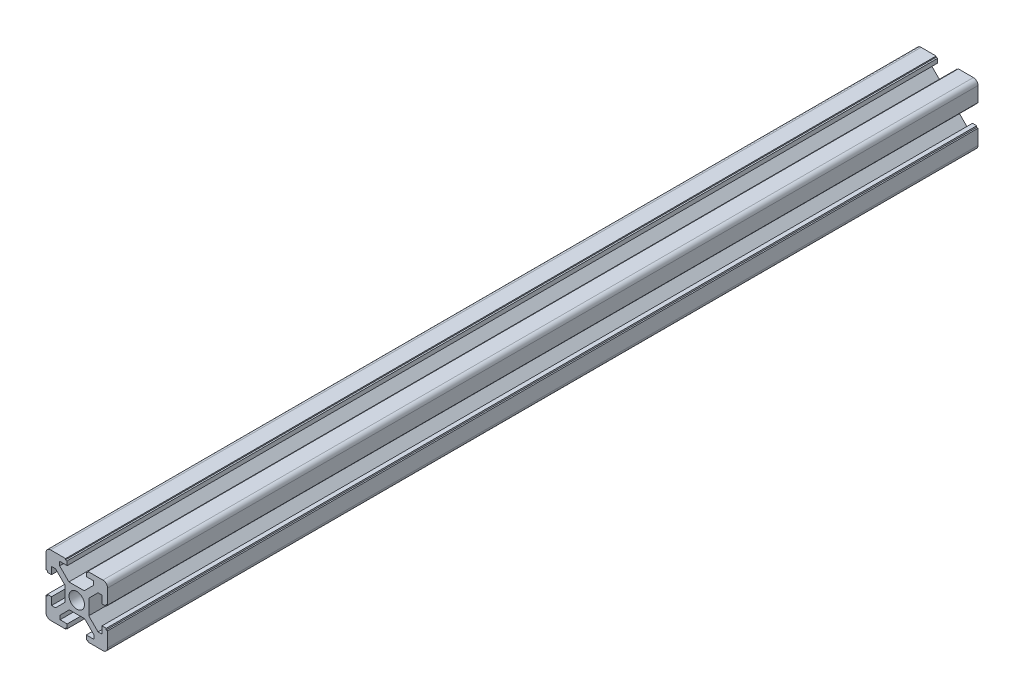
SolidWorks part; units mm, degrees
ref_plane "Front Plane" through (0, 0, 0) normal (0, 0, 1) x (1, 0, 0)
ref_plane "Top Plane" through (0, 0, 0) normal (0, 1, 0) x (1, 0, 0)
ref_plane "Right Plane" through (0, 0, 0) normal (1, 0, 0) x (0, 0, -1)
sketch "Sketch1" plane through (0, 0, 0) normal (0, 0, 1) x (1, 0, 0)
  line L0 (240.9169, 601.7923) -> (1204.5843, 601.7923) construction
  line L6 (13.0291, 10.3872) -> (13.0291, 12.8554)
  line L7 (12.7291, 6.0212) -> (29.7291, 6.0212)
  line L11 (11.2291, 7.5212) -> (11.2291, 24.3895)
  line L12 (12.7291, 25.8895) -> (29.7291, 25.8895)
  line L13 (31.2291, 7.5212) -> (31.2291, 24.3895)
  line L14 (11.2291, 6.0212) -> (31.2291, 25.8895) construction
  line L15 (11.2291, 25.8895) -> (31.2291, 6.0212) construction
  line L16 (13.0291, 24.0895) -> (13.041, 24.0895)
  line L17 (29.4291, 10.5205) -> (29.4291, 12.8554)
  line L18 (13.0291, 7.8212) -> (13.041, 7.8212)
  line L19 (11.2291, 15.9554) -> (31.2291, 15.9554) construction
  line L20 (11.6567, 12.8554) -> (13.0291, 12.8554)
  line L21 (11.6567, 19.0554) -> (13.0291, 19.0554)
  line L22 (21.2291, 6.0212) -> (21.2291, 25.8895) construction
  line L23 (24.8338, 25.9554) -> (24.8338, 25.5277)
  line L24 (17.3291, 21.0535) -> (17.3291, 19.8297)
  line L25 (11.2291, 19.56) -> (11.6567, 19.56)
  line L26 (11.6567, 19.56) -> (11.6567, 19.0554)
  line L27 (11.6567, 19.0554) -> (13.0291, 19.0554)
  line L28 (17.3291, 18.3778) -> (14.3166, 21.3903)
  line L29 (14.3166, 21.3903) -> (13.0291, 21.3903)
  line L30 (17.3291, 13.3997) -> (14.3166, 10.3872)
  line L31 (14.3166, 10.3872) -> (13.0291, 10.3872)
  line L32 (13.0291, 7.8212) -> (13.0291, 24.0895) construction
  line L33 (29.4172, 7.8212) -> (29.4291, 7.8212)
  line L34 (13.0291, 7.8212) -> (29.4291, 7.8212) construction
  line L35 (17.3291, 12.081) -> (17.3291, 10.641)
  line L36 (24.8338, 25.5277) -> (24.3291, 25.5277)
  line L37 (11.2291, 12.8554) -> (31.2291, 12.8554) construction
  line L38 (24.3291, 25.5277) -> (24.3291, 24.1554)
  line L39 (11.2291, 19.0554) -> (31.2291, 19.0554) construction
  line L40 (17.3291, 18.3778) -> (17.3291, 13.3997)
  line L41 (11.6567, 12.8554) -> (11.6567, 12.3367)
  line L42 (11.6567, 12.3367) -> (11.2291, 12.3367)
  line L43 (13.0291, 19.0554) -> (13.0291, 21.3903)
  line L44 (24.3291, 24.1554) -> (26.664, 24.1554)
  line L45 (26.664, 22.8679) -> (26.664, 24.1554)
  line L46 (23.6515, 19.8554) -> (26.664, 22.8679)
  line L47 (23.6515, 19.8554) -> (18.6734, 19.8554)
  line L48 (18.6734, 19.8554) -> (15.661, 22.8679)
  line L49 (15.661, 24.1554) -> (18.1291, 24.1554)
  line L50 (15.661, 22.8679) -> (15.661, 24.1554)
  line L51 (18.1291, 25.5277) -> (18.1291, 24.1554)
  line L52 (18.1291, 25.5277) -> (17.6104, 25.5277)
  line L53 (17.6104, 25.5277) -> (17.6104, 25.9554)
  line L54 (31.2291, 12.3507) -> (30.8015, 12.3507)
  line L55 (30.8015, 12.3507) -> (30.8015, 12.8554)
  line L56 (30.8015, 12.8554) -> (29.4291, 12.8554)
  line L57 (29.4291, 12.8554) -> (29.4291, 10.5205)
  line L58 (28.1416, 10.5205) -> (29.4291, 10.5205)
  line L59 (25.1291, 13.533) -> (28.1416, 10.5205)
  line L60 (25.1291, 13.533) -> (25.1291, 18.511)
  line L61 (25.1291, 18.511) -> (28.1416, 21.5235)
  line L62 (29.4291, 21.5235) -> (29.4291, 19.0554)
  line L63 (28.1416, 21.5235) -> (29.4291, 21.5235)
  line L64 (30.8015, 19.0554) -> (29.4291, 19.0554)
  line L65 (30.8015, 19.0554) -> (30.8015, 19.5741)
  line L66 (30.8015, 19.5741) -> (31.2291, 19.5741)
  line L67 (17.6244, 5.9554) -> (17.6244, 6.383)
  line L68 (17.6244, 6.383) -> (18.1291, 6.383)
  line L69 (18.1291, 6.383) -> (18.1291, 7.7554)
  line L70 (18.1291, 7.7554) -> (15.7942, 7.7554)
  line L71 (15.7942, 9.0429) -> (15.7942, 7.7554)
  line L72 (18.8067, 12.0554) -> (15.7942, 9.0429)
  line L73 (18.8067, 12.0554) -> (23.7848, 12.0554)
  line L74 (23.7848, 12.0554) -> (26.7973, 9.0429)
  line L75 (26.7973, 7.7554) -> (24.3291, 7.7554)
  line L76 (26.7973, 9.0429) -> (26.7973, 7.7554)
  line L77 (24.3291, 6.383) -> (24.3291, 7.7554)
  line L78 (24.3291, 6.383) -> (24.8478, 6.383)
  line L79 (24.8478, 6.383) -> (24.8478, 5.9554)
  line L80 (29.4172, 24.0895) -> (29.4291, 24.0895)
  line L81 (13.0291, 24.0895) -> (29.4291, 24.0895) construction
  line L82 (29.4291, 19.0554) -> (29.4291, 21.5235)
  line L83 (29.4291, 7.8212) -> (29.4291, 24.0895) construction
  circle A1 centre (21.2291, 15.9554) radius 2.5
  arc A2 (12.7291, 25.8895) -> (11.2291, 24.3895) centre (12.7291, 24.3895) ccw
  arc A3 (11.2291, 7.5212) -> (12.7291, 6.0212) centre (12.7291, 7.5212) ccw
  arc A4 (29.7291, 6.0212) -> (31.2291, 7.5212) centre (29.7291, 7.5212) ccw
  arc A5 (31.2291, 24.3895) -> (29.7291, 25.8895) centre (29.7291, 24.3895) ccw
  arc A6 (13.0291, 24.0895) -> (13.0291, 24.0895) centre (13.0291, 24.0895) ccw
  arc A7 (29.4291, 24.0895) -> (29.4291, 24.0895) centre (29.4291, 24.0895) ccw
  arc A8 (29.4291, 7.8212) -> (29.4291, 7.8212) centre (29.4291, 7.8212) ccw
  arc A9 (13.0291, 7.8212) -> (13.0291, 7.8212) centre (13.0291, 7.8212) ccw
  point P105 (21.2291, 15.9554)
  dimension "D1" = 20
  dimension "D2" = 1.5
  dimension "D3" = 1.5
  dimension "D7" = 4
  dimension "D8" = 6.1
  dimension "D4" = 1.8
  dimension "D5" = 3.1
  dimension "D6" = 3.1
extrude "Boss-Extrude1" add sketch "Sketch1" along normal blind 283
